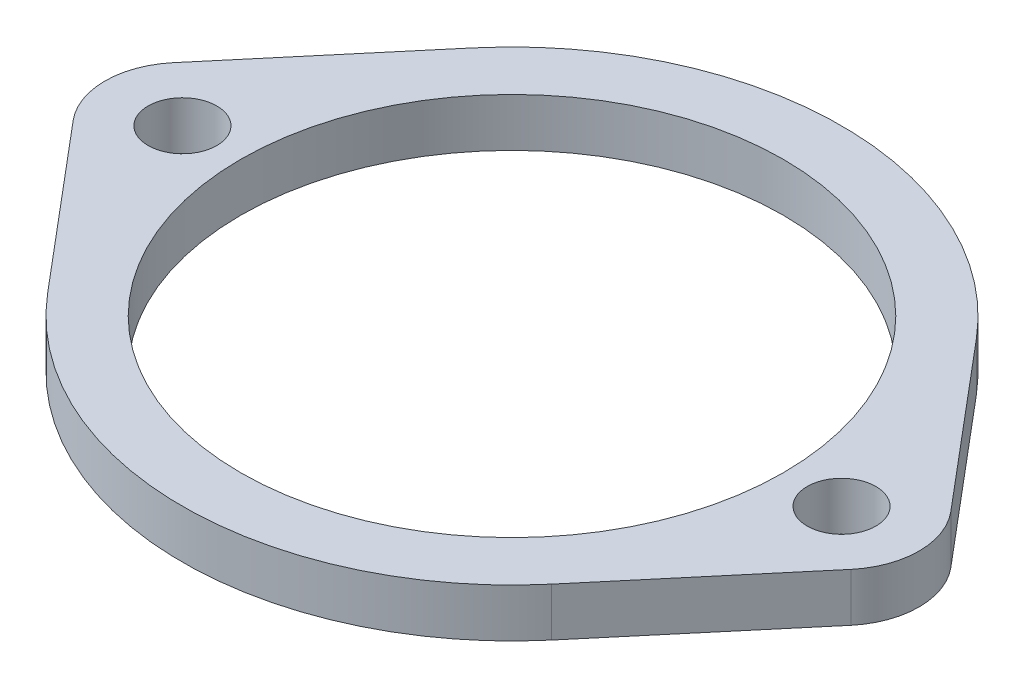
SolidWorks part; units mm, degrees
ref_plane "Front Plane" through (0, 0, 0) normal (0, 0, 1) x (1, 0, 0)
ref_plane "Top Plane" through (0, 0, 0) normal (0, 1, 0) x (1, 0, 0)
ref_plane "Right Plane" through (0, 0, 0) normal (1, 0, 0) x (0, 0, -1)
sketch "Sketch1" plane through (0, 0, 0) normal (0, 1, 0) x (1, 0, 0)
  line L0 (26.67, 43.18) -> (26.67, 0) construction
  line L1 (0, 0) -> (53.34, 0) construction
  line L2 (0, 0) -> (0, 43.18) construction
  line L3 (0, 43.18) -> (53.34, 43.18) construction
  line L4 (53.34, 0) -> (53.34, 43.18) construction
  line L5 (0, 21.59) -> (53.34, 21.59) construction
  line L6 (1.1953, 24.8634) -> (10.16, 35.5022)
  line L7 (1.1953, 18.3166) -> (10.16, 7.6778)
  line L8 (52.1447, 18.3166) -> (43.18, 7.6778)
  line L9 (52.1447, 24.8634) -> (43.18, 35.5022)
  circle A0 centre (5.08, 21.59) radius 2.25
  circle A1 centre (48.26, 21.59) radius 2.25
  circle A2 centre (26.67, 21.59) radius 17.78
  circle A3 centre (26.67, 21.59) radius 21.59 construction
  circle A4 centre (5.08, 21.59) radius 5.08 construction
  arc A5 (1.1953, 18.3166) -> (1.1953, 24.8634) centre (5.08, 21.59) cw
  arc A6 (10.16, 35.5022) -> (43.18, 35.5022) centre (26.67, 21.59) cw
  arc A7 (10.16, 7.6778) -> (43.18, 7.6778) centre (26.67, 21.59) ccw
  arc A8 (52.1447, 18.3166) -> (52.1447, 24.8634) centre (48.26, 21.59) ccw
  dimension "D3" = 4.5
  dimension "D5" = 35.56
  dimension "D6" = 43.18
  dimension "D7" = 10.16
  dimension "D1" = 43.18
  dimension "D2" = 53.34
  dimension "D4" = 21.59
extrude "Boss-Extrude1" add sketch "Sketch1" along normal blind 3.175 contours L8 A8 L9 A6 L6 A5 L7 A7 A1 A0 A2
sketch "Sketch4" plane through (0, 0, 0) normal (0, -1, 0) x (-1, 0, 0)
  line L0 (-26.67, 0) -> (-26.67, 43.18) construction
  line L1 (-53.34, 21.59) -> (0, 21.59) construction
  arc A0 (-43.18, 7.6778) -> (-10.16, 7.6778) centre (-26.67, 21.59) ccw construction
  arc A1 (-10.16, 35.5022) -> (-43.18, 35.5022) centre (-26.67, 21.59) ccw construction
  arc A2 (-52.1447, 24.8634) -> (-52.1447, 18.3166) centre (-48.26, 21.59) ccw construction
  arc A3 (-1.1953, 18.3166) -> (-1.1953, 24.8634) centre (-5.08, 21.59) ccw construction
equation "\"D1@Boss-Extrude1\"=0.9-1/8-0.65"
